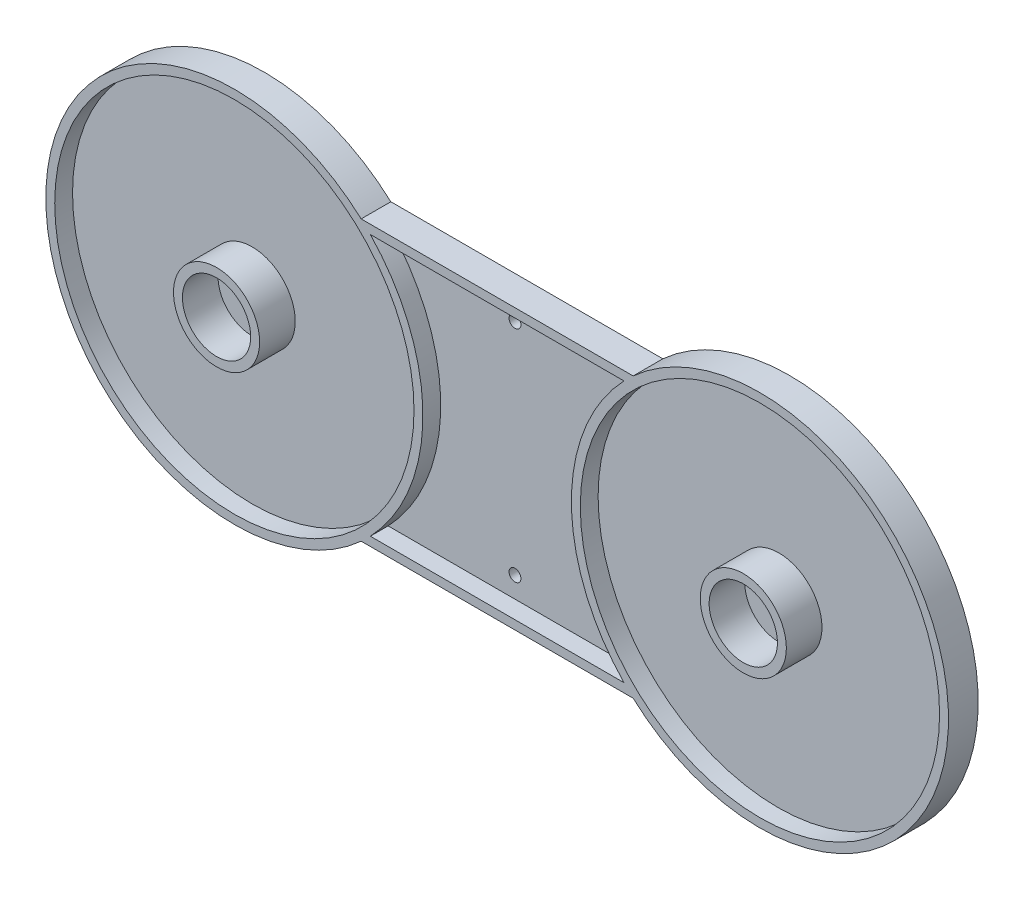
SolidWorks part; units mm, degrees
material "Chrome Stainless Steel"
ref_plane "Front Plane" through (0, 0, 0) normal (0, 0, 1) x (1, 0, 0)
ref_plane "Top Plane" through (0, 0, 0) normal (0, 1, 0) x (1, 0, 0)
ref_plane "Right Plane" through (0, 0, 0) normal (1, 0, 0) x (0, 0, -1)
sketch "Sketch3" plane through (0, 0, 0) normal (0, 0, 1) x (1, 0, 0)
  line L0 (0, 0) -> (-44.25, 0) construction
  line L1 (0, 0) -> (44.25, 0) construction
  line L2 (0, -23.5) -> (0, 23.5) construction
  line L3 (22.9002, 23.5) -> (-22.9002, 23.5)
  line L4 (22.9002, -23.5) -> (-22.9002, -23.5)
  arc A0 (-22.9002, 23.5) -> (-22.9002, -23.5) centre (-44.25, 0) ccw
  arc A1 (22.9002, -23.5) -> (22.9002, 23.5) centre (44.25, 0) ccw
  point P6 (-80.6153, -13.317)
  dimension "D4" = 63.5
  dimension "D5" = 63.5
  dimension "D1" = 23.5
  dimension "D3" = 44.25
extrude "Boss-Extrude1" add sketch "Sketch3" along normal blind 2
sketch "Sketch5" plane through (0, 0, 2) normal (0, 0, 1) x (1, 0, 0)
  line L0 (-23.488, -22) -> (23.488, -22) construction
  line L1 (21.3576, 22) -> (-21.3576, 22) construction
  line L2 (22.9002, 23.5) -> (-22.9002, 23.5)
  line L3 (-22.9002, -23.5) -> (22.9002, -23.5)
  line L4 (22.9002, 23.5) -> (-22.9002, 23.5)
  line L5 (-22.9002, -23.5) -> (22.9002, -23.5)
  line L6 (-21.3576, 22) -> (21.3576, 22)
  line L7 (-21.3576, -22) -> (21.3576, -22)
  line L9 (23.488, 22) -> (-23.488, 22) construction
  arc A0 (-23.488, 22) -> (-23.488, -22) centre (-44.25, 0) ccw construction
  arc A1 (23.488, -22) -> (23.488, 22) centre (44.25, 0) ccw construction
  arc A2 (22.9002, -23.5) -> (22.9002, 23.5) centre (44.25, 0) ccw
  arc A3 (-22.9002, 23.5) -> (-22.9002, -23.5) centre (-44.25, 0) ccw
  circle A6 centre (-44.25, 0) radius 30.25
  circle A7 centre (44.25, 0) radius 30.25
  arc A8 (-21.3576, -22) -> (-21.3576, 22) centre (-44.25, 0) ccw
  arc A9 (22.9002, -23.5) -> (22.9002, 23.5) centre (44.25, 0) ccw
  arc A10 (-22.9002, 23.5) -> (-22.9002, -23.5) centre (-44.25, 0) ccw construction
  arc A11 (22.9002, -23.5) -> (22.9002, 23.5) centre (44.25, 0) ccw construction
  arc A12 (-22.9002, 23.5) -> (-22.9002, -23.5) centre (-44.25, 0) ccw
  arc A13 (21.3576, 22) -> (21.3576, -22) centre (44.25, 0) ccw
  point P15 (-20.8854, -22)
  point P19 (-102.5781, -16.3482)
  point P21 (0, 0)
  point P22 (0, 0)
  point P23 (0, 0)
  dimension "D1" = 0
  dimension "D2" = 1.5
extrude "Boss-Extrude2" add sketch "Sketch5" along normal blind 3
sketch "Sketch6" plane through (0, 0, 2) normal (0, 0, 1) x (1, 0, 0)
  circle A0 centre (-44.25, 0) radius 7.25
  circle A1 centre (-44.25, 0) radius 5.75
  circle A2 centre (44.4471, -0.2865) radius 7.25
  circle A3 centre (44.4471, -0.2865) radius 5.75
  circle A5 centre (-44.25, 0) radius 30.25 construction
  point P4 (44.25, 0)
  point P5 (0, 0)
  dimension "D1" = 14.5
  dimension "D2" = 11.5
  dimension "D3" = 14.5
  dimension "D4" = 11.5
  dimension "D5" = 88.6971
  dimension "D6" = 0.2865
extrude "Boss-Extrude3" add sketch "Sketch6" along normal blind 6
sketch "Sketch7" plane through (0, 0, 2) normal (0, 0, 1) x (1, 0, 0)
  line L0 (22.9002, 23.5) -> (-22.9002, 23.5) construction
  line L1 (0, 0) -> (0, 18.5) construction
  line L2 (-3.6341, 0) -> (4.921, 0) construction
  circle A0 centre (0, 18.5) radius 1
  circle A1 centre (0, -18.5) radius 1
  dimension "D1" = 5
  dimension "D2" = 2
extrude "Cut-Extrude1" cut sketch "Sketch7" against normal through all and the other way blind 10
